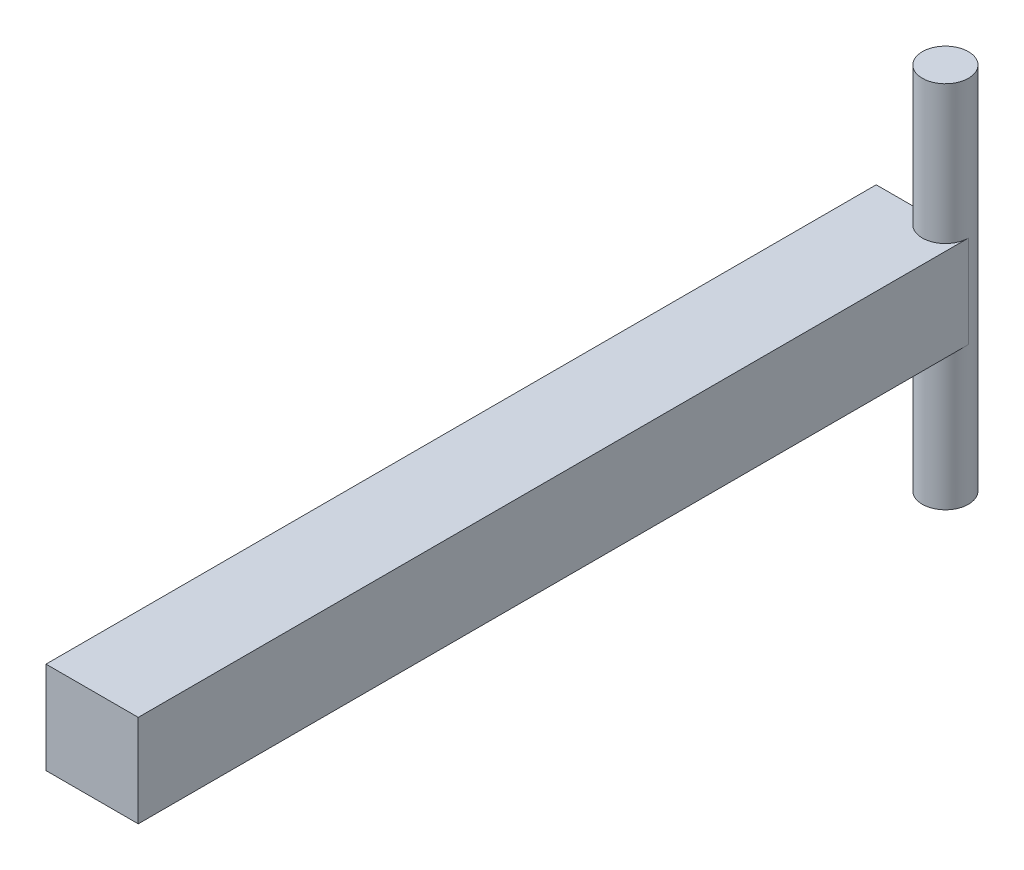
SolidWorks part; units mm, degrees
ref_plane "Front" through (0, 0, 0) normal (0, 0, 1) x (1, 0, 0)
ref_plane "Top" through (0, 0, 0) normal (0, 1, 0) x (1, 0, 0)
ref_plane "Right" through (0, 0, 0) normal (1, 0, 0) x (0, 0, -1)
sketch "草图1" plane through (0, 0, 0) normal (0, 0, 1) x (1, 0, 0)
  line L1 (-2, 2) -> (2, 2)
  line L2 (-2, 2) -> (-2, -2)
  line L3 (-2, -2) -> (2, -2)
  line L4 (2, 2) -> (2, -2)
  dimension "D1" = 4
  dimension "D2" = 4
  dimension "D3" = 2
  dimension "D4" = 2
extrude "凸台-拉伸1" add sketch "草图1" along normal blind 36
sketch "草图3" plane through (0, 0, 0) normal (0, 1, 0) x (1, 0, 0)
  line L0 (2, 0) -> (-2, 0) construction
  circle A0 centre (1, 0) radius 1
extrude "凸台-拉伸2" add sketch "草图3" along normal mid plane 16
